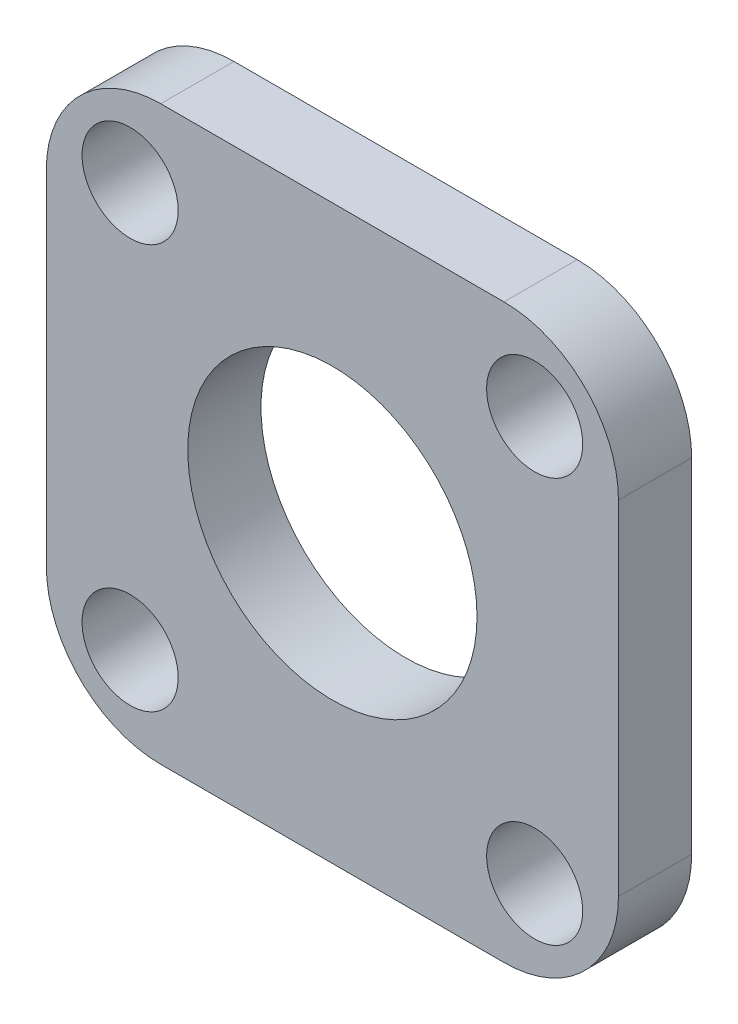
SolidWorks part; units mm, degrees
ref_plane "Front Plane" through (0, 0, 0) normal (0, 0, 1) x (1, 0, 0)
ref_plane "Top Plane" through (0, 0, 0) normal (0, 1, 0) x (1, 0, 0)
ref_plane "Right Plane" through (0, 0, 0) normal (1, 0, 0) x (0, 0, -1)
sketch "Sketch1" plane through (0, 0, 0) normal (0, 0, 1) x (1, 0, 0)
  line L1 (-12.5, 12.5) -> (12.5, 12.5)
  line L2 (-12.5, 12.5) -> (-12.5, -12.5)
  line L3 (-12.5, -12.5) -> (12.5, -12.5)
  line L4 (12.5, 12.5) -> (12.5, -12.5)
  line L5 (-12.5, 12.5) -> (12.5, -12.5) construction
  line L6 (-12.5, -12.5) -> (12.5, 12.5) construction
  point P0 (0, 0)
  dimension "D1" = 25
  dimension "D2" = 25
extrude "Boss-Extrude1" add sketch "Sketch1" along normal blind 3.2
sketch "Sketch2" plane through (0, 0, 3.2) normal (0, 0, 1) x (1, 0, 0)
  circle A0 centre (0, 0) radius 6.32
extrude "Cut-Extrude1" cut sketch "Sketch2" against normal up to next
sketch "Sketch3" plane through (0, 0, 3.2) normal (0, 0, 1) x (1, 0, 0)
  line L0 (-12.5, 12.5) -> (0, 0) construction
  circle A0 centre (-8.8388, 8.8388) radius 2.1
  dimension "D1" = 4.2
  dimension "D2" = 12.5
extrude "Cut-Extrude2" cut sketch "Sketch3" against normal through all
pattern_circular "CirPattern1" count 4 every 90 about axis through (0, 0, 0) along (0, 0, 1) of "Cut-Extrude2"
fillet "Fillet2" radius 5 4 edges at (-12.5, -12.5, 1.6) (12.5, -12.5, 1.6) (12.5, 12.5, 1.6) (-12.5, 12.5, 1.6)
